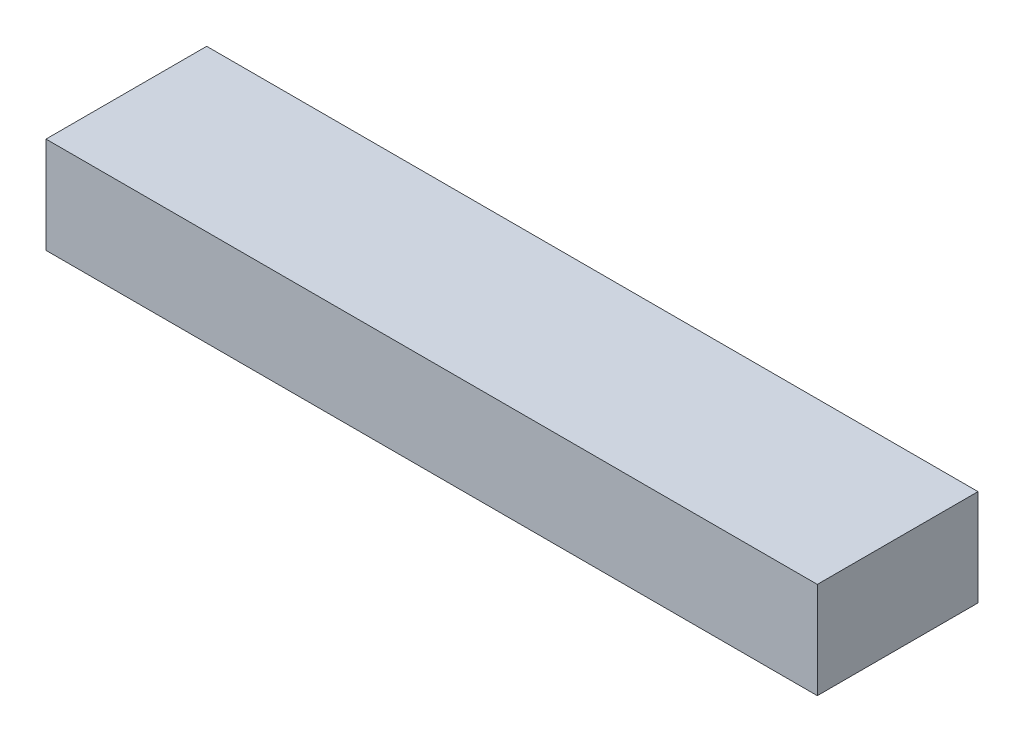
SolidWorks part; units mm, degrees
ref_plane "Front Plane" through (0, 0, 0) normal (0, 0, 1) x (1, 0, 0)
ref_plane "Top Plane" through (0, 0, 0) normal (0, 1, 0) x (1, 0, 0)
ref_plane "Right Plane" through (0, 0, 0) normal (1, 0, 0) x (0, 0, -1)
sketch "Sketch1" plane through (0, 0, 0) normal (1, 0, 0) x (0, 0, -1)
  line L1 (0, 0) -> (63.5, 0)
  line L2 (0, 0) -> (0, -38.1)
  line L3 (0, -38.1) -> (63.5, -38.1)
  line L4 (63.5, 0) -> (63.5, -38.1)
  dimension "D1" = 38.1
  dimension "D2" = 63.5
extrude "Boss-Extrude1" add sketch "Sketch1" along normal blind 304.8
